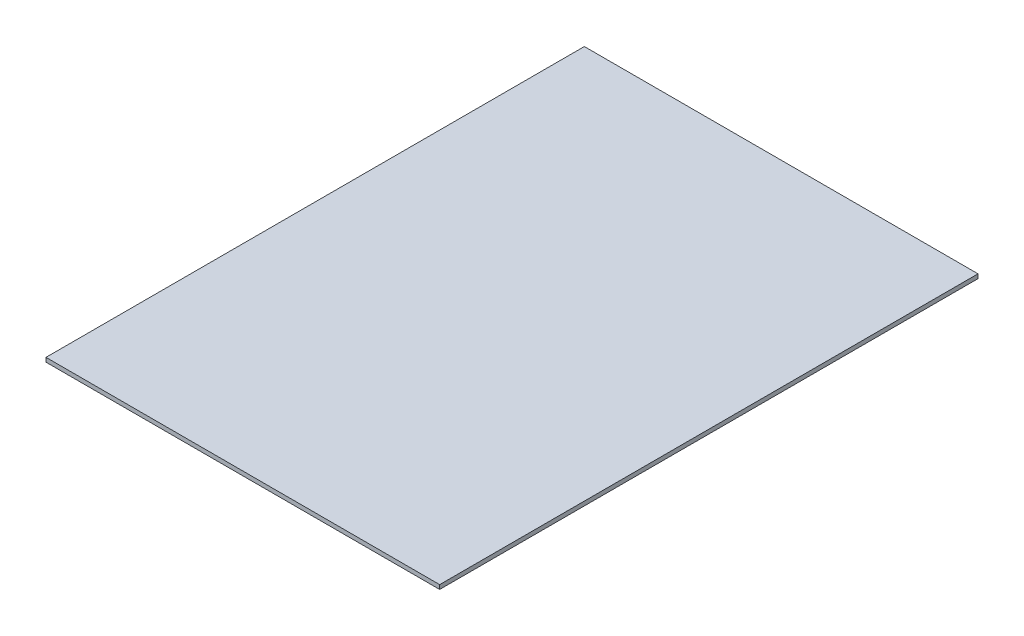
SolidWorks part; units mm, degrees
ref_plane "Спереди" through (0, 0, 0) normal (0, 0, 1) x (1, 0, 0)
ref_plane "Сверху" through (0, 0, 0) normal (0, 1, 0) x (1, 0, 0)
ref_plane "Справа" through (0, 0, 0) normal (1, 0, 0) x (0, 0, -1)
sketch "Эскиз1" plane through (0, 0, 0) normal (0, 1, 0) x (1, 0, 0)
  line L1 (-117, -160) -> (117, -160)
  line L2 (-117, -160) -> (-117, 160)
  line L3 (-117, 160) -> (117, 160)
  line L4 (117, -160) -> (117, 160)
  line L5 (-117, -160) -> (117, 160) construction
  line L6 (-117, 160) -> (117, -160) construction
  point P0 (0, 0)
extrude "Бобышка-Вытянуть1" add sketch "Эскиз1" along normal blind 2.5
